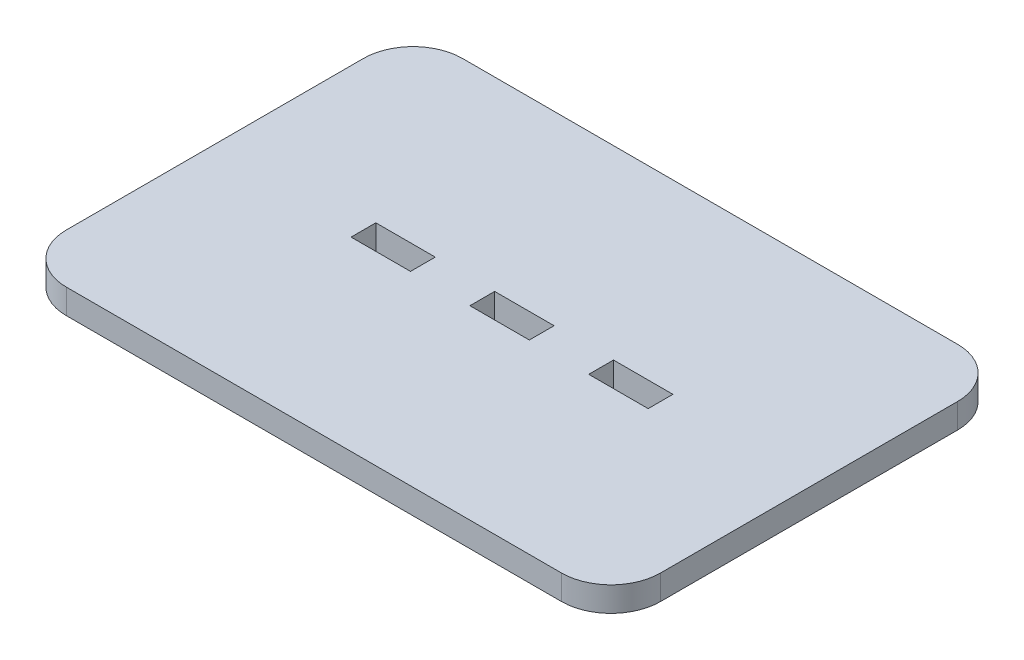
SolidWorks part; units mm, degrees
ref_plane "Front Plane" through (0, 0, 0) normal (0, 0, 1) x (1, 0, 0)
ref_plane "Top Plane" through (0, 0, 0) normal (0, 1, 0) x (1, 0, 0)
ref_plane "Right Plane" through (0, 0, 0) normal (1, 0, 0) x (0, 0, -1)
sketch "Sketch1" plane through (0, 0, 0) normal (0, 1, 0) x (1, 0, 0)
  line L1 (-50, 40) -> (50, 40)
  line L2 (-60, 30) -> (-60, -30)
  line L3 (-50, -40) -> (50, -40)
  line L4 (60, 30) -> (60, -30)
  line L5 (-60, 40) -> (-3.75, 2.5) construction
  line L6 (-60, -40) -> (-3.75, -2.5) construction
  line L7 (-30, 2.5) -> (-18, 2.5)
  line L8 (-30, 2.5) -> (-30, -2.5)
  line L9 (-30, -2.5) -> (-18, -2.5)
  line L10 (30, 2.5) -> (30, -2.5)
  line L11 (3.75, 2.5) -> (60, 40) construction
  line L12 (3.75, -2.5) -> (60, -40) construction
  line L13 (-6, 2.5) -> (6, 2.5)
  line L15 (18, 2.5) -> (30, 2.5)
  line L16 (-18, 2.5) -> (-18, -2.5)
  line L17 (-6, 2.5) -> (-6, -2.5)
  line L18 (6, 2.5) -> (6, -2.5)
  line L19 (18, 2.5) -> (18, -2.5)
  line L20 (-6, -2.5) -> (6, -2.5)
  line L21 (18, -2.5) -> (30, -2.5)
  arc A0 (50, 40) -> (60, 30) centre (50, 30) cw
  arc A1 (60, -30) -> (50, -40) centre (50, -30) cw
  arc A2 (-50, -40) -> (-60, -30) centre (-50, -30) cw
  arc A3 (-50, 40) -> (-60, 30) centre (-50, 30) ccw
  point P0 (0, 0)
  point P6 (0, 0)
  dimension "D5" = 10
  dimension "D1" = 120
  dimension "D2" = 80
  dimension "D3" = 60
  dimension "D4" = 5
extrude "Boss-Extrude1" add sketch "Sketch1" along normal blind 5
